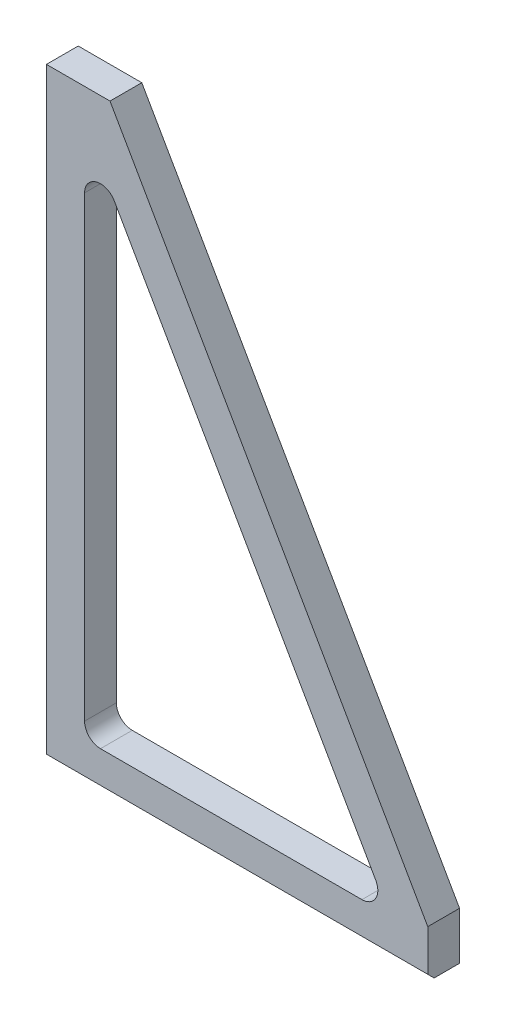
SolidWorks part; units mm, degrees
ref_plane "Front" through (0, 0, 0) normal (0, 0, 1) x (1, 0, 0)
ref_plane "Top" through (0, 0, 0) normal (0, 1, 0) x (1, 0, 0)
ref_plane "Right" through (0, 0, 0) normal (1, 0, 0) x (0, 0, -1)
sketch "Sketch1" plane through (0, 0, 0) normal (0, 0, 1) x (1, 0, 0)
  line L0 (15.24, 21.59) -> (15.24, 204.4515)
  line L1 (0, 0) -> (152.4, 0)
  line L2 (0, 0) -> (0, 241.3)
  line L3 (0, 241.3) -> (25.4, 241.3)
  line L4 (152.4, 0) -> (152.4, 19.05)
  line L7 (21.59, 15.24) -> (126.0823, 15.24)
  line L8 (25.4, 241.3) -> (152.4, 19.05)
  line L9 (27.1033, 207.6019) -> (131.5956, 24.7405)
  arc A0 (131.5956, 24.7405) -> (126.0823, 15.24) centre (126.0823, 21.59) cw
  arc A3 (15.24, 21.59) -> (21.59, 15.24) centre (21.59, 21.59) ccw
  arc A4 (15.24, 204.4515) -> (27.1033, 207.6019) centre (21.59, 204.4515) cw
  dimension "D4" = 6.35
  dimension "D8" = 6.35
  dimension "D9" = 6.35
  dimension "D1" = 152.4
  dimension "D2" = 241.3
  dimension "D5" = 19.05
  dimension "D6" = 25.4
  dimension "D3" = 15.24
  dimension "D7" = 15.24
extrude "Base-Extrude" add sketch "Sketch1" along normal blind 12.7
chamfer "Chamfer2" distance 2.54 angle 45 1 edges at (76.2, 0, 12.7)
